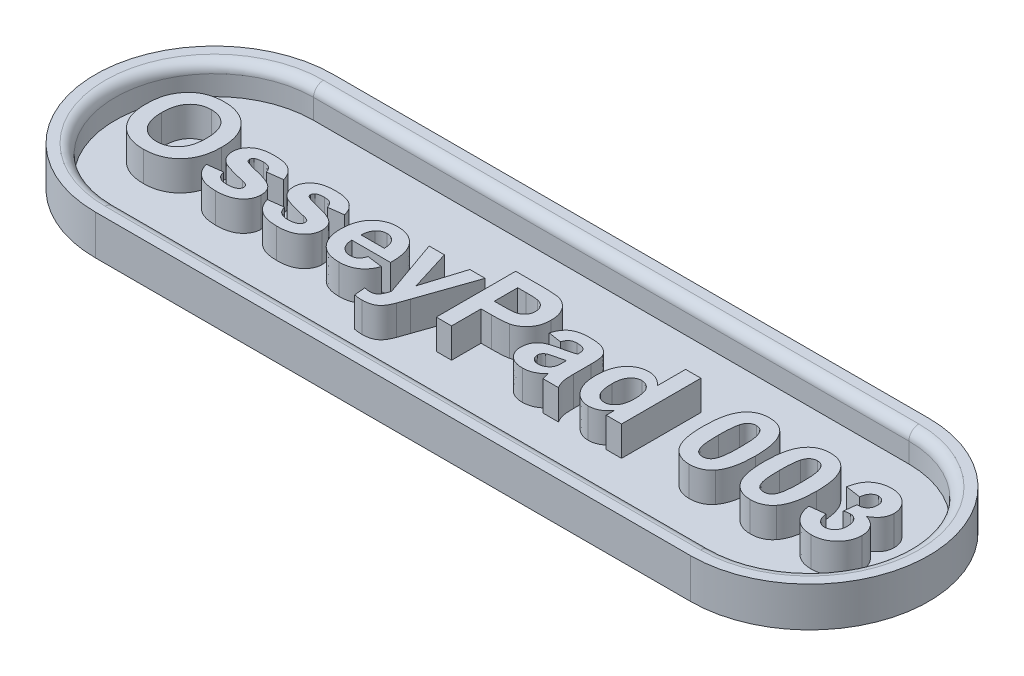
SolidWorks part; units mm, degrees
ref_plane "Front Plane" through (0, 0, 0) normal (0, 0, 1) x (1, 0, 0)
ref_plane "Top Plane" through (0, 0, 0) normal (0, 1, 0) x (1, 0, 0)
ref_plane "Right Plane" through (0, 0, 0) normal (1, 0, 0) x (0, 0, -1)
sketch "Sketch1" plane through (0, 0, 0) normal (0, 1, 0) x (1, 0, 0)
  line L0 (-15, 0) -> (15, 0) construction
  line L1 (-15, 6) -> (15, 6)
  line L2 (-15, -6) -> (15, -6)
  arc A0 (-15, 6) -> (-15, -6) centre (-15, 0) ccw
  arc A1 (15, -6) -> (15, 6) centre (15, 0) ccw
  point P2 (0, 0)
  dimension "D1" = 12
  dimension "D2" = 30
extrude "Boss-Extrude1" add sketch "Sketch1" along normal blind 2
sketch "Sketch2" plane through (0, 2, 0) normal (0, 1, 0) x (1, 0, 0)
  line L0 (-15, 0) -> (15, 0) construction
  line L1 (-15, 5) -> (15, 5)
  line L2 (-15, -5) -> (15, -5)
  arc A0 (-15, 5) -> (-15, -5) centre (-15, 0) ccw
  arc A1 (15, -5) -> (15, 5) centre (15, 0) ccw
  point P2 (0, 0)
  dimension "D1" = 30
  dimension "D2" = 10
extrude "Cut-Extrude1" cut sketch "Sketch2" against normal blind 1.5
sketch "Sketch3" plane through (0, 0.5, 0) normal (0, 1, 0) x (1, 0, 0)
  line L0 (-21, -1.995) -> (21, -1.995) construction
  line L1 (0, -8.7006) -> (0, 6.9821) construction
  line L3 (-15, -5) -> (15, -5) construction
  text T0 "OsseyPad 003" font "Arial" height 4
  dimension "D1" = 3.005
extrude "Boss-Extrude2" add sketch "Sketch3" along normal blind 1.5
fillet "Fillet1" radius 0.5 4 edges at (0, 2, -5) (20, 2, 0) (0, 2, 5) (-20, 2, 0)
